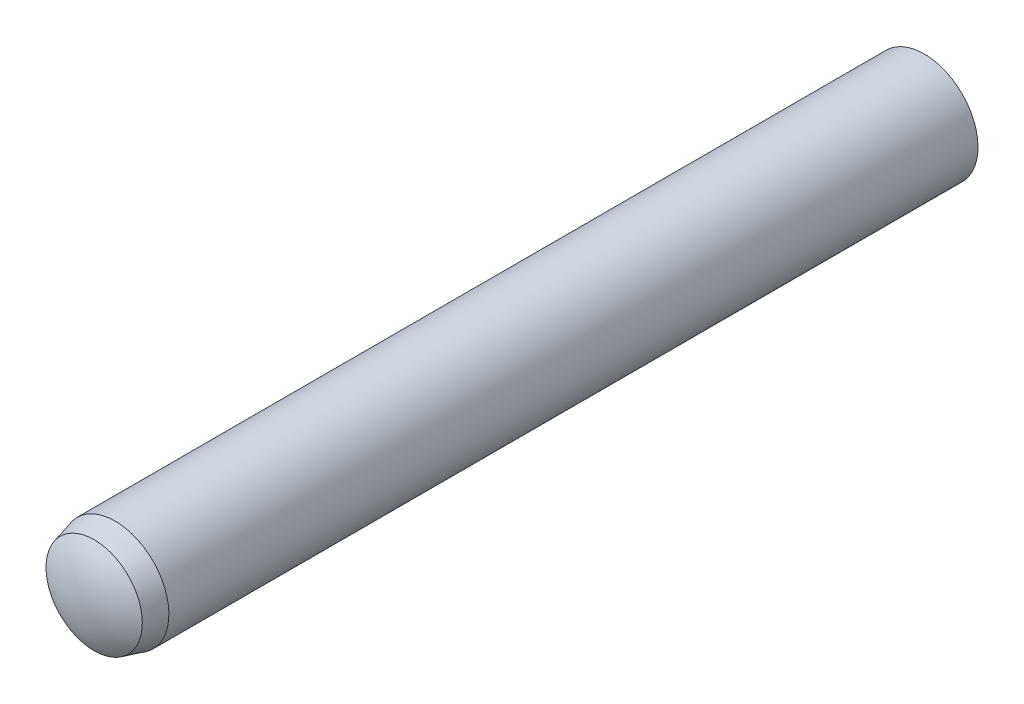
SolidWorks part; units mm, degrees
material "Alloy Steel"
ref_plane "Front Plane" through (0, 0, 0) normal (0, 0, 1) x (1, 0, 0)
ref_plane "Top Plane" through (0, 0, 0) normal (0, 1, 0) x (1, 0, 0)
ref_plane "Right Plane" through (0, 0, 0) normal (1, 0, 0) x (0, 0, -1)
sketch "Sketch1" plane through (0, 0, 0) normal (0, 0, 1) x (1, 0, 0)
  circle A0 centre (0, 0) radius 5
  point P3 (0, 5)
  dimension "Diameter" = 10
sketch "Sketch2" plane through (0, 0, 0) normal (1, 0, 0) x (0, 0, -1)
  line L0 (-40, 0) -> (40, 0) construction
  line L1 (-40, 0) -> (-40, 5) construction
  line L2 (-40, 5) -> (40, 5)
  line L3 (40, 5) -> (40, 0) construction
  line L4 (-38.7, 4.4775) -> (-36.75, 5)
  arc A0 (-40, 0) -> (-38.7, 4.4775) centre (-31.6392, 0) cw
  arc A1 (40, 0) -> (38.5, 5) centre (30.9167, 0) ccw
  point P2 (0, 0)
  point P11 (-30, 0)
  point P13 (30, 0)
  dimension "Length" = 80
  dimension "D1" = 15
  dimension "D2" = 1.5
  dimension "D3" = 3.25
  dimension "D4" = 1.95
  dimension "D5" = 10
  dimension "D6" = 10
sketch "Sketch3" plane through (0, 0, 0) normal (1, 0, 0) x (0, 0, -1)
  line L0 (-40, 0) -> (40, 0) construction
  line L1 (-38.7, 4.4775) -> (-36.75, 5) construction
  line L2 (-40, 0) -> (40, 0)
  line L3 (-38.7, 4.4775) -> (-36.75, 5)
  line L4 (-36.75, 5) -> (38.5, 5)
  arc A0 (40, 0) -> (38.5, 5) centre (30.9167, 0) ccw construction
  arc A1 (-38.7, 4.4775) -> (-40, 0) centre (-31.6392, 0) ccw construction
  arc A2 (40, 0) -> (38.5, 5) centre (30.9167, 0) ccw
  arc A3 (-38.7, 4.4775) -> (-40, 0) centre (-31.6392, 0) ccw
revolve "Revolve1" add sketch "Sketch3" angle 360 about L2
equation "\"D2@Sketch2\" = \"Diameter@Sketch1\" * .15"
equation "\"D3@Sketch2\" = \"Diameter@Sketch1\" * .325"
equation "\"D4@Sketch2\" = \"D3@Sketch2\" * .6"
equation "\"D5@Sketch2\"=\"Diameter@Sketch1\""
equation "\"D6@Sketch2\"=\"D5@sketch2\""
